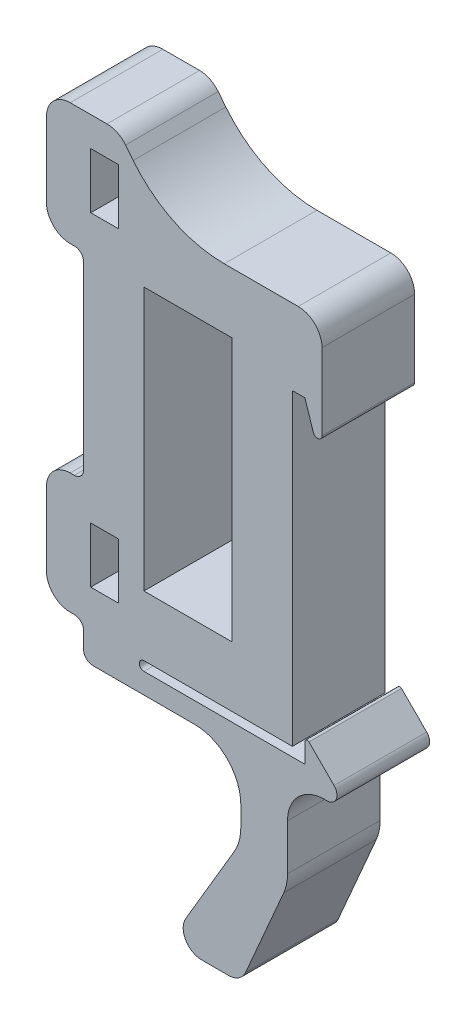
SolidWorks part; units mm, degrees
ref_plane "Front Plane" through (0, 0, 0) normal (0, 0, 1) x (1, 0, 0)
ref_plane "Top Plane" through (0, 0, 0) normal (0, 1, 0) x (1, 0, 0)
ref_plane "Right Plane" through (0, 0, 0) normal (1, 0, 0) x (0, 0, -1)
sketch "Sketch2" plane through (0, 0, 0) normal (0, 0, 1) x (1, 0, 0)
  line L26 (0, 66.6518) -> (0, 33.3918)
  line L27 (0, 66.6518) -> (1.3474, 66.6518)
  line L29 (3.1939, 72.2618) -> (3.1939, 64.0167)
  line L30 (1.3474, 66.6518) -> (2.26, 63.8675)
  line L32 (-22.54, 67.4018) -> (-22.54, 47.9618)
  line L33 (0, 33.3918) -> (-16.03, 33.3918)
  line L34 (-16.03, 68.3218) -> (-6.51, 68.3218)
  line L35 (-16.03, 68.3218) -> (-16.03, 39.9018)
  line L36 (-16.03, 39.9018) -> (-6.51, 39.9018)
  line L37 (-6.51, 68.3218) -> (-6.51, 39.9018)
  line L39 (1.3522, 32.3918) -> (1.3522, 34.5182)
  line L40 (1.7789, 34.6951) -> (4.4968, 31.982)
  line L42 (3.7479, 30.1718) -> (3.4703, 30.1718)
  line L43 (1.3522, 32.3918) -> (-16.03, 32.3918)
  line L47 (-22.54, 32.9426) -> (-22.54, 31.1718)
  line L48 (-21.7699, 78.3926) -> (-21.7699, 72.3926)
  line L49 (-21.7699, 37.3926) -> (-18.7599, 37.3926)
  line L50 (-18.7599, 37.3926) -> (-18.7599, 43.3926)
  line L51 (-18.7599, 78.3926) -> (-21.7699, 78.3926)
  line L52 (-23.54, 68.4018) -> (-23.9846, 68.4018)
  line L54 (-26.5546, 77.4018) -> (-26.5546, 70.9718)
  line L55 (-21.7699, 72.3926) -> (-18.7599, 72.3926)
  line L56 (-21.7699, 43.3926) -> (-21.7699, 37.3926)
  line L57 (-21.7699, 43.3926) -> (-18.7599, 43.3926)
  line L58 (-18.7599, 72.3926) -> (-18.7599, 78.3926)
  line L60 (-26.5546, 44.3918) -> (-26.5546, 36.5126)
  line L61 (-0.5297, 26.1718) -> (-0.5297, 21.2082)
  line L62 (-10.5728, 30.1718) -> (-21.54, 30.1718)
  line L63 (-5.5728, 22.9844) -> (-5.5728, 25.1718)
  line L65 (-26.5546, 77.4018) -> (-26.5546, 79.0009)
  line L66 (-0.9417, 19.2207) -> (-5.0508, 9.7353)
  line L67 (-6.2659, 20.4446) -> (-11.5133, 11.5462)
  line L68 (-9.7906, 8.5303) -> (-6.886, 8.5303)
  line L71 (-23.9846, 81.5709) -> (-20.0216, 81.5709)
  line L73 (0.6239, 74.8318) -> (-7.3575, 74.8318)
  line L74 (-17.1909, 79.5718) -> (-18.0111, 80.6018)
  line L76 (-23.9846, 46.9618) -> (-23.54, 46.9618)
  line L78 (-23.9846, 33.9426) -> (-23.54, 33.9426)
  arc A1 (1.7789, 34.6951) -> (1.3522, 34.5182) centre (1.6022, 34.5182) ccw
  arc A2 (3.7479, 30.1718) -> (4.4968, 31.982) centre (3.7479, 31.2318) ccw
  arc A4 (2.26, 63.8675) -> (3.1939, 64.0167) centre (2.715, 64.0167) ccw
  arc A6 (-16.03, 33.3918) -> (-16.03, 32.3918) centre (-16.03, 32.8918) ccw
  arc A7 (-18.0111, 80.6018) -> (-20.0216, 81.5709) centre (-20.0216, 79.0009) ccw
  arc A8 (-7.3575, 74.8318) -> (-17.1909, 79.5718) centre (-7.3575, 87.4018) cw
  arc A9 (0.6239, 74.8318) -> (3.1939, 72.2618) centre (0.6239, 72.2618) cw
  arc A10 (-26.5546, 79.0009) -> (-23.9846, 81.5709) centre (-23.9846, 79.0009) cw
  arc A11 (-23.9846, 68.4018) -> (-26.5546, 70.9718) centre (-23.9846, 70.9718) cw
  arc A12 (-22.54, 67.4018) -> (-23.54, 68.4018) centre (-23.54, 67.4018) ccw
  arc A13 (-26.5546, 44.3918) -> (-23.9846, 46.9618) centre (-23.9846, 44.3918) cw
  arc A14 (-23.9846, 33.9426) -> (-26.5546, 36.5126) centre (-23.9846, 36.5126) cw
  arc A15 (-23.54, 33.9426) -> (-22.54, 32.9426) centre (-23.54, 32.9426) cw
  arc A16 (-22.54, 31.1718) -> (-21.54, 30.1718) centre (-21.54, 31.1718) ccw
  arc A17 (-22.54, 47.9618) -> (-23.54, 46.9618) centre (-23.54, 47.9618) cw
  arc A18 (-5.5728, 25.1718) -> (-10.5728, 30.1718) centre (-10.5728, 25.1718) ccw
  arc A19 (-6.2659, 20.4446) -> (-5.5728, 22.9844) centre (-10.5728, 22.9844) ccw
  arc A20 (-9.7906, 8.5303) -> (-11.5133, 11.5462) centre (-9.7906, 10.5303) cw
  arc A21 (-5.0508, 9.7353) -> (-6.886, 8.5303) centre (-6.886, 10.5303) cw
  arc A22 (-0.5297, 21.2082) -> (-0.9417, 19.2207) centre (-5.5297, 21.2082) cw
  arc A23 (-0.5297, 26.1718) -> (3.4703, 30.1718) centre (3.4703, 26.1718) cw
  point P38 (-21.7699, 40.3926)
  point P46 (-21.7699, 75.3926)
  point P73 (-5.5728, 30.1718)
  dimension "D6" = 0.25
  dimension "D7" = 1.06
  dimension "D13" = 12.57
  dimension "D10" = 2.57
  dimension "D15" = 2.57
  dimension "D16" = 2.57
  dimension "D17" = 2.57
  dimension "D18" = 1
  dimension "D19" = 2.57
  dimension "D20" = 2.57
  dimension "D21" = 1
  dimension "D22" = 1
  dimension "D23" = 5
  dimension "D24" = 5
  dimension "D25" = 2
  dimension "D26" = 2
  dimension "D27" = 5
  dimension "D28" = 4
  dimension "D1" = 2.26
  dimension "D2" = 6.51
  dimension "D3" = 6.51
  dimension "D4" = 6.51
  dimension "D5" = 9.52
  dimension "D8" = 6.51
  dimension "D9" = 1
  dimension "D11" = 28.42
  dimension "D12" = 33.26
  dimension "D14" = 35
extrude "Boss-Extrude1" add sketch "Sketch2" along normal blind 10
sketch "Sketch4" plane through (-26.5546, 0, 0) normal (-1, 0, 0) x (0, 0, 1)
  line L0 (5, 79.0009) -> (5, 11.5462) construction
  line L1 (10, 79.0009) -> (0, 79.0009) construction
  line L2 (10, 11.5462) -> (0, 11.5462) construction
  circle A0 centre (5, 75.4522) radius 1.8525
  circle A1 centre (5, 40.4522) radius 1.8525
  dimension "D1" = 35
extrude "Cut-Extrude1" cut sketch "Sketch4" against normal blind 9.5
